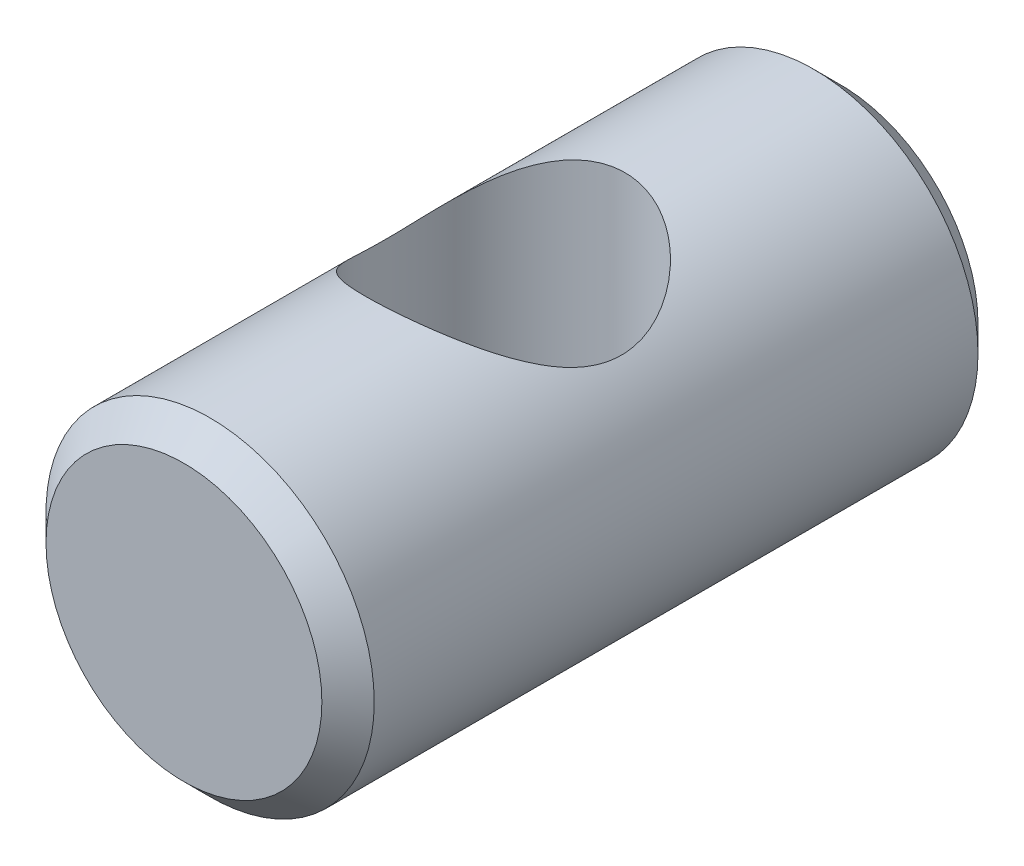
SolidWorks part; units mm, degrees
ref_plane "Front Plane" through (0, 0, 0) normal (0, 0, 1) x (1, 0, 0)
ref_plane "Top Plane" through (0, 0, 0) normal (0, 1, 0) x (1, 0, 0)
ref_plane "Right Plane" through (0, 0, 0) normal (1, 0, 0) x (0, 0, -1)
sketch "Sketch1" plane through (0, 0, 0) normal (0, 0, 1) x (1, 0, 0)
  circle A0 centre (0, 0) radius 4.765
  dimension "D1" = 9.53
extrude "Boss-Extrude1" add sketch "Sketch1" along normal mid plane 19.05
chamfer "Chamfer1" distance 0.76 angle 45 2 edges at (4.765, 0, -9.525) (4.765, 0, 9.525)
sketch "Sketch2" plane through (0, 0, 0) normal (0, 1, 0) x (1, 0, 0)
  circle A0 centre (-0.25, 0) radius 3.43
  dimension "D1" = 6.86
  dimension "D2" = 0.25
extrude "Cut-Extrude1" cut sketch "Sketch2" against normal through all both and the other way through all
